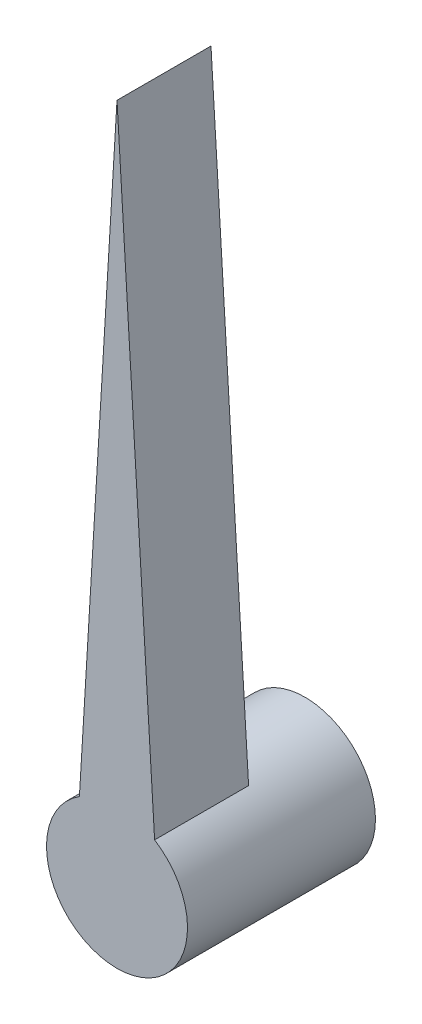
SolidWorks part; units mm, degrees
ref_plane "Front Plane" through (0, 0, 0) normal (0, 0, 1) x (1, 0, 0)
ref_plane "Top Plane" through (0, 0, 0) normal (0, 1, 0) x (1, 0, 0)
ref_plane "Right Plane" through (0, 0, 0) normal (1, 0, 0) x (0, 0, -1)
sketch "Sketch1" plane through (0, 0, 0) normal (0, 0, 1) x (1, 0, 0)
  circle A0 centre (0, 0) radius 3.81
  dimension "D1" = 7.62
extrude "Boss-Extrude2" add sketch "Sketch1" along normal blind 10.16
sketch "Sketch4" plane through (0, 0, 10.16) normal (0, 0, 1) x (1, 0, 0)
  line L0 (-2.0323, 3.2227) -> (2.0323, 3.2227)
  line L1 (0, 36.83) -> (-2.0323, 3.2227)
  line L2 (0, 36.83) -> (2.0323, 3.2227)
  circle A0 centre (0, 0) radius 3.81 construction
extrude "Boss-Extrude3" add sketch "Sketch4" against normal blind 5.08
sketch "Sketch5" plane through (0, 0, 0) normal (0, 0, -1) x (-1, 0, 0)
  circle A0 centre (0, 0) radius 2.413
  dimension "D1" = 4.826
extrude "Cut-Extrude1" cut sketch "Sketch5" against normal blind 5.08
